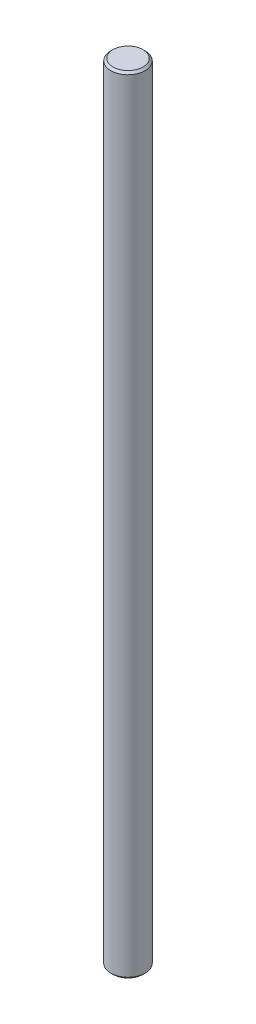
SolidWorks part; units mm, degrees
ref_plane "Front Plane" through (0, 0, 0) normal (0, 0, 1) x (1, 0, 0)
ref_plane "Top Plane" through (0, 0, 0) normal (0, 1, 0) x (1, 0, 0)
ref_plane "Right Plane" through (0, 0, 0) normal (1, 0, 0) x (0, 0, -1)
sketch "Sketch1" plane through (0, 0, 0) normal (0, 0, 1) x (1, 0, 0)
  line L0 (0, 0) -> (0, 183) construction
  line L1 (0, 0) -> (8, 0) construction
  line L2 (8, -182) -> (8, 182)
  line L3 (8, 182) -> (7, 183)
  line L4 (7, 183) -> (0, 183)
  line L5 (7, -183) -> (0, -183)
  line L6 (8, -182) -> (7, -183)
  line L7 (0, 183) -> (0, -183)
  dimension "D1" = 16
  dimension "D2" = 45
  dimension "D3" = 1
  dimension "D4" = 366
revolve "Revolve1" add sketch "Sketch1" angle 360 about L7
